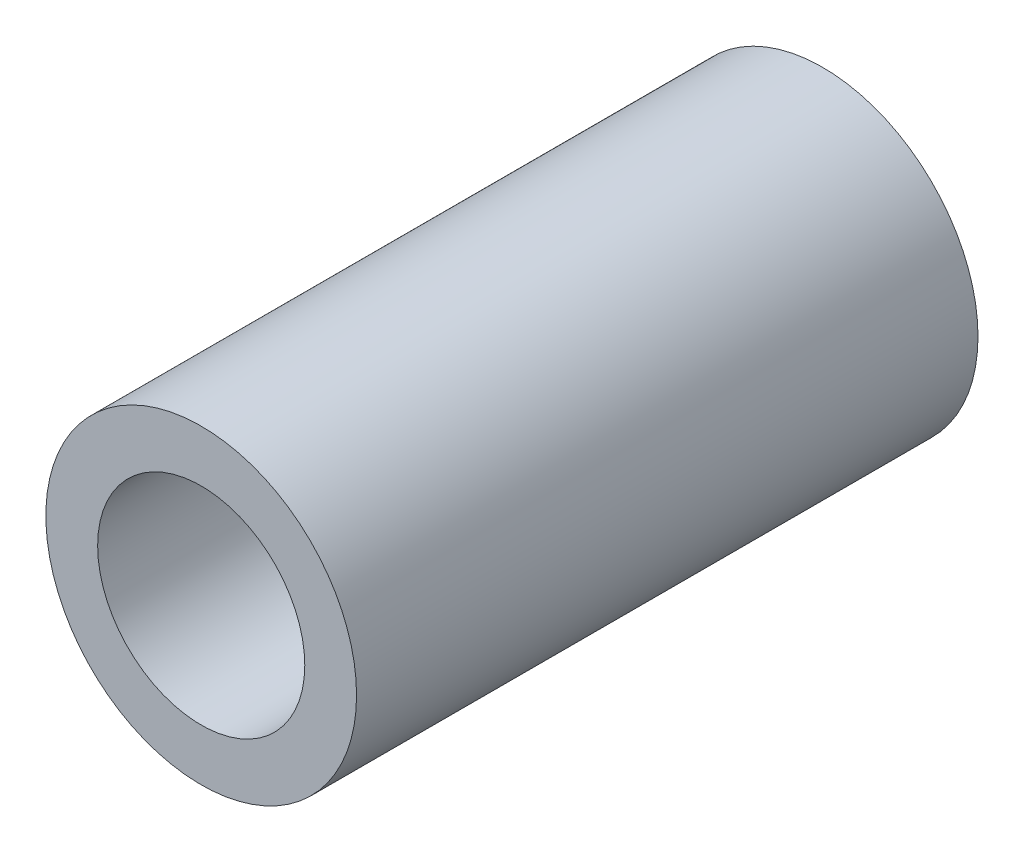
SolidWorks part; units mm, degrees
material "Nylon 101"
ref_plane "Front Plane" through (0, 0, 0) normal (0, 0, 1) x (1, 0, 0)
ref_plane "Top Plane" through (0, 0, 0) normal (0, 1, 0) x (1, 0, 0)
ref_plane "Right Plane" through (0, 0, 0) normal (1, 0, 0) x (0, 0, -1)
sketch "Sketch1" plane through (0, 0, 0) normal (0, 0, 1) x (1, 0, 0)
  circle A0 centre (0, 0) radius 4.7625
  circle A1 centre (0, 0) radius 3.175
  dimension "D1" = 6.35
  dimension "D2" = 9.525
extrude "Boss-Extrude1" add sketch "Sketch1" along normal blind 19.05
